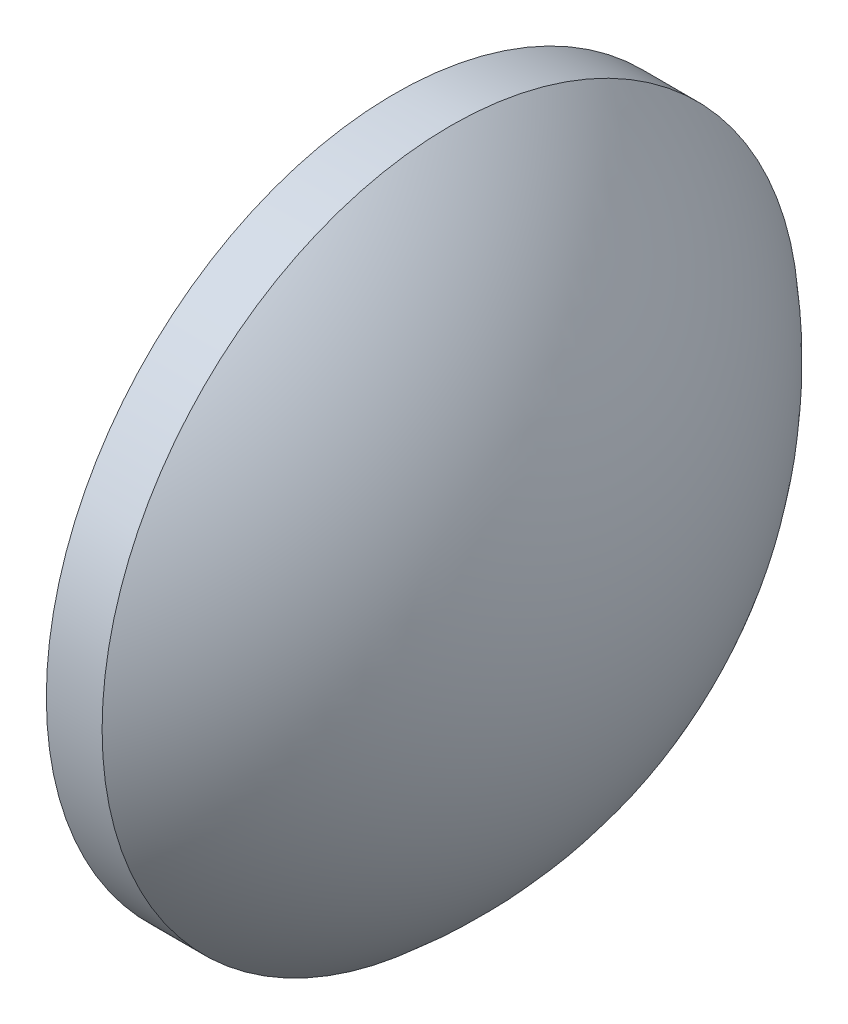
SolidWorks part; units mm, degrees
ref_plane "前视基准面" through (0, 0, 0) normal (0, 0, 1) x (1, 0, 0)
ref_plane "上视基准面" through (0, 0, 0) normal (0, 1, 0) x (1, 0, 0)
ref_plane "右视基准面" through (0, 0, 0) normal (1, 0, 0) x (0, 0, -1)
sketch "草图1" plane through (0, 0, 0) normal (0, 0, 1) x (1, 0, 0)
  line L0 (539.6031, 132.5985) -> (553.0489, 132.5985) construction
  line L1 (541.1152, 132.5985) -> (541.1152, 145.0985)
  line L2 (548.9752, 132.5985) -> (541.1152, 132.5985)
  line L5 (541.1152, 145.0985) -> (543.1152, 145.0985)
  arc A0 (548.9752, 132.5985) -> (543.1152, 145.0985) centre (532.7132, 132.5985) ccw
revolve "旋转1" add sketch "草图1" angle 360 about L0
